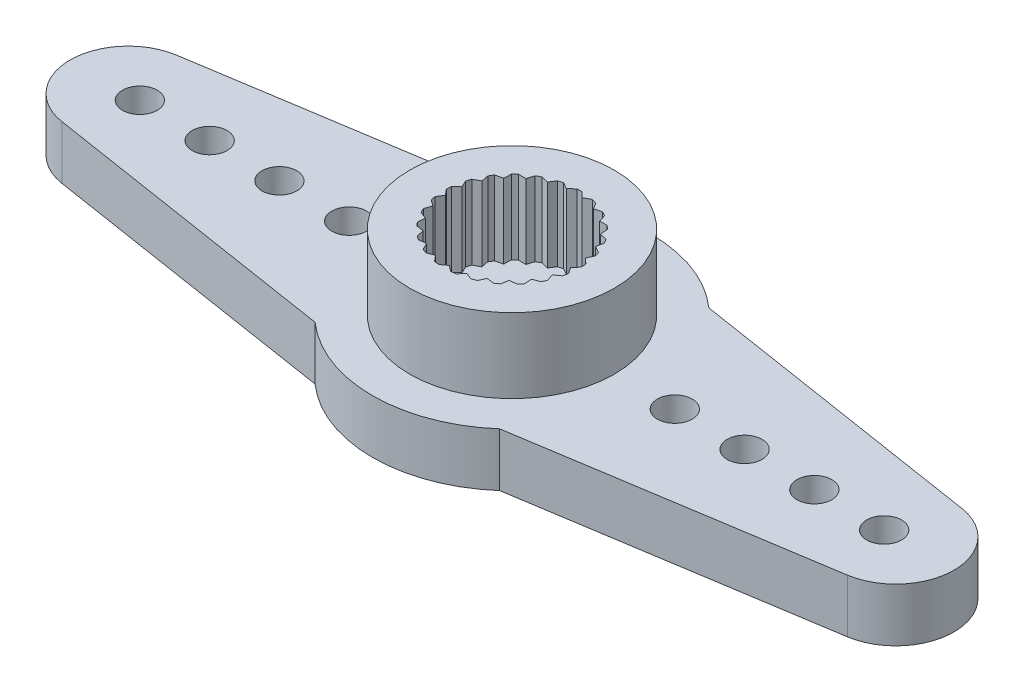
SolidWorks part; units mm, degrees
ref_plane "Front Plane" through (0, 0, 0) normal (0, 0, 1) x (1, 0, 0)
ref_plane "Top Plane" through (0, 0, 0) normal (0, 1, 0) x (1, 0, 0)
ref_plane "Right Plane" through (0, 0, 0) normal (1, 0, 0) x (0, 0, -1)
ref_plane "Plane1" through (0, 1.15, 0) normal (0, 1, 0) x (1, 0, 0)
sketch "Sketch1" plane through (0, 1.15, 0) normal (0, 1, 0) x (1, 0, 0)
  line L0 (-3.9686, 4.5) -> (-16.8881, 2.4697)
  line L1 (-16.8881, -2.4697) -> (-3.9686, -4.5)
  line L2 (3.9686, -4.5) -> (16.8881, -2.4697)
  line L3 (16.8881, 2.4697) -> (3.9686, 4.5)
  arc A0 (3.9686, 4.5) -> (-3.9686, 4.5) centre (0, 0) ccw
  arc A1 (-16.8881, 2.4697) -> (-16.8881, -2.4697) centre (-16.5, 0) ccw
  arc A2 (-3.9686, -4.5) -> (3.9686, -4.5) centre (0, 0) ccw
  arc A3 (16.8881, -2.4697) -> (16.8881, 2.4697) centre (16.5, 0) ccw
extrude "Boss-Extrude1" add sketch "Sketch1" against normal blind 2.3
sketch "Sketch2" plane through (0, 1.15, 0) normal (0, 1, 0) x (-1, 0, 0)
  circle A0 centre (0, 0) radius 4.4
extrude "Boss-Extrude2" add sketch "Sketch2" along normal blind 3.2
sketch "Sketch3" plane through (0, 4.35, 0) normal (0, 1, 0) x (-1, 0, 0)
  line L0 (-0.6167, -2.8337) -> (-0.3384, -2.6787)
  line L1 (-0.3384, -2.6787) -> (-0.1074, -2.898)
  line L2 (0.1074, -2.898) -> (0.3384, -2.6787)
  line L3 (0.3384, -2.6787) -> (0.6167, -2.8337)
  line L4 (0.8248, -2.7802) -> (0.9939, -2.5104)
  line L5 (0.9939, -2.5104) -> (1.302, -2.5913)
  line L6 (1.4903, -2.4878) -> (1.587, -2.1843)
  line L7 (1.587, -2.1843) -> (1.9055, -2.1861)
  line L8 (2.0621, -2.039) -> (2.0804, -1.721)
  line L9 (2.0804, -1.721) -> (2.3893, -1.6435)
  line L10 (2.5044, -1.4621) -> (2.443, -1.1496)
  line L11 (2.443, -1.1496) -> (2.723, -0.9977)
  line L12 (2.7894, -0.7934) -> (2.6522, -0.5059)
  line L13 (2.6522, -0.5059) -> (2.8855, -0.2892)
  line L14 (2.899, -0.0748) -> (2.6947, 0.1695)
  line L15 (2.6947, 0.1695) -> (2.8668, 0.4375)
  line L16 (2.8265, 0.6486) -> (2.5679, 0.8343)
  line L17 (2.5679, 0.8343) -> (2.6679, 1.1367)
  line L18 (2.5765, 1.3311) -> (2.2797, 1.4467)
  line L19 (2.2797, 1.4467) -> (2.3014, 1.7645)
  line L20 (2.1645, 1.93) -> (1.8483, 1.9682)
  line L21 (1.8483, 1.9682) -> (1.7903, 2.2814)
  line L22 (1.6165, 2.4077) -> (1.3007, 2.366)
  line L23 (1.3007, 2.366) -> (1.1667, 2.655)
  line L24 (0.967, 2.734) -> (0.6715, 2.6152)
  line L25 (0.6715, 2.6152) -> (0.4698, 2.8617)
  line L26 (0.2566, 2.8886) -> (0, 2.7)
  line L27 (0, 2.7) -> (-0.2566, 2.8886)
  line L28 (-0.4698, 2.8617) -> (-0.6715, 2.6152)
  line L29 (-0.6715, 2.6152) -> (-0.967, 2.734)
  line L30 (-1.1667, 2.655) -> (-1.3007, 2.366)
  line L31 (-1.3007, 2.366) -> (-1.6165, 2.4077)
  line L32 (-1.7903, 2.2814) -> (-1.8483, 1.9682)
  line L33 (-1.8483, 1.9682) -> (-2.1645, 1.93)
  line L34 (-2.3014, 1.7645) -> (-2.2797, 1.4467)
  line L35 (-2.2797, 1.4467) -> (-2.5765, 1.3311)
  line L36 (-2.6679, 1.1367) -> (-2.5679, 0.8343)
  line L37 (-2.5679, 0.8343) -> (-2.8265, 0.6486)
  line L38 (-2.8668, 0.4375) -> (-2.6947, 0.1695)
  line L39 (-2.6947, 0.1695) -> (-2.899, -0.0748)
  line L40 (-2.8855, -0.2892) -> (-2.6522, -0.5059)
  line L41 (-2.6522, -0.5059) -> (-2.7894, -0.7934)
  line L42 (-2.723, -0.9977) -> (-2.443, -1.1496)
  line L43 (-2.443, -1.1496) -> (-2.5044, -1.4621)
  line L44 (-2.3893, -1.6435) -> (-2.0804, -1.721)
  line L45 (-2.0804, -1.721) -> (-2.0621, -2.039)
  line L46 (-1.9055, -2.1861) -> (-1.587, -2.1843)
  line L47 (-1.587, -2.1843) -> (-1.4903, -2.4878)
  line L48 (-1.302, -2.5913) -> (-0.9939, -2.5104)
  line L49 (-0.9939, -2.5104) -> (-0.8248, -2.7802)
  arc A0 (-0.8248, -2.7802) -> (-0.6167, -2.8337) centre (0, 0) ccw
  arc A1 (-0.1074, -2.898) -> (0.1074, -2.898) centre (0, 0) ccw
  arc A2 (0.6167, -2.8337) -> (0.8248, -2.7802) centre (0, 0) ccw
  arc A3 (1.302, -2.5913) -> (1.4903, -2.4878) centre (0, 0) ccw
  arc A4 (1.9055, -2.1861) -> (2.0621, -2.039) centre (0, 0) ccw
  arc A5 (2.3893, -1.6435) -> (2.5044, -1.4621) centre (0, 0) ccw
  arc A6 (2.723, -0.9977) -> (2.7894, -0.7934) centre (0, 0) ccw
  arc A7 (2.8855, -0.2892) -> (2.899, -0.0748) centre (0, 0) ccw
  arc A8 (2.8668, 0.4375) -> (2.8265, 0.6486) centre (0, 0) ccw
  arc A9 (2.6679, 1.1367) -> (2.5765, 1.3311) centre (0, 0) ccw
  arc A10 (2.3014, 1.7645) -> (2.1645, 1.93) centre (0, 0) ccw
  arc A11 (1.7903, 2.2814) -> (1.6165, 2.4077) centre (0, 0) ccw
  arc A12 (1.1667, 2.655) -> (0.967, 2.734) centre (0, 0) ccw
  arc A13 (0.4698, 2.8617) -> (0.2566, 2.8886) centre (0, 0) ccw
  arc A14 (-0.2566, 2.8886) -> (-0.4698, 2.8617) centre (0, 0) ccw
  arc A15 (-0.967, 2.734) -> (-1.1667, 2.655) centre (0, 0) ccw
  arc A16 (-1.6165, 2.4077) -> (-1.7903, 2.2814) centre (0, 0) ccw
  arc A17 (-2.1645, 1.93) -> (-2.3014, 1.7645) centre (0, 0) ccw
  arc A18 (-2.5765, 1.3311) -> (-2.6679, 1.1367) centre (0, 0) ccw
  arc A19 (-2.8265, 0.6486) -> (-2.8668, 0.4375) centre (0, 0) ccw
  arc A20 (-2.899, -0.0748) -> (-2.8855, -0.2892) centre (0, 0) ccw
  arc A21 (-2.7894, -0.7934) -> (-2.723, -0.9977) centre (0, 0) ccw
  arc A22 (-2.5044, -1.4621) -> (-2.3893, -1.6435) centre (0, 0) ccw
  arc A23 (-2.0621, -2.039) -> (-1.9055, -2.1861) centre (0, 0) ccw
  arc A24 (-1.4903, -2.4878) -> (-1.302, -2.5913) centre (0, 0) ccw
extrude "Cut-Extrude1" cut sketch "Sketch3" against normal blind 3.2
hole_wizard "Ø1.5 (1.5) Diameter Hole1" positions "Sketch5" profile "Sketch4" hole size "Ø1.5" standard "ANSI Metric"
sketch "Sketch5" plane through (0, -1.15, 0) normal (0, -1, 0) x (-1, 0, 0)
  point P0 (-7, 0)
  point P1 (-16, 0)
  point P2 (-13, 0)
  point P3 (-10, 0)
  point P4 (7, 0)
  point P5 (16, 0)
  point P6 (13, 0)
  point P7 (10, 0)
sketch "Sketch4" plane through (7, -1.15, 0) normal (1, 0, 0) x (0, 0, -1)
  line L0 (0, 0) -> (0, 5.5)
  line L1 (0, 5.5) -> (0.75, 5.5)
  line L2 (0.75, 5.5) -> (0.75, 0)
  line L5 (0.75, 0) -> (0, 0)
  line L11 (0, -6.35) -> (0, 107.95) construction
  dimension "Thru Hole Dia." = 1.5
  dimension "Thru Hole Depth" = 5.5
hole_wizard "Ø3.0 (3) Diameter Hole1" positions "Sketch7" profile "Sketch6" hole size "Ø3.0" standard "ANSI Metric"
sketch "Sketch7" plane through (0, -1.15, 0) normal (0, -1, 0) x (-1, 0, 0)
  point P0 (0, 0)
sketch "Sketch6" plane through (0, -1.15, 0) normal (1, 0, 0) x (0, 0, -1)
  line L0 (0, 0) -> (0, 5.5)
  line L1 (0, 5.5) -> (1.5, 5.5)
  line L2 (1.5, 5.5) -> (1.5, 0)
  line L5 (1.5, 0) -> (0, 0)
  line L11 (0, -6.35) -> (0, 107.95) construction
  dimension "Thru Hole Dia." = 3
  dimension "Thru Hole Depth" = 5.5
